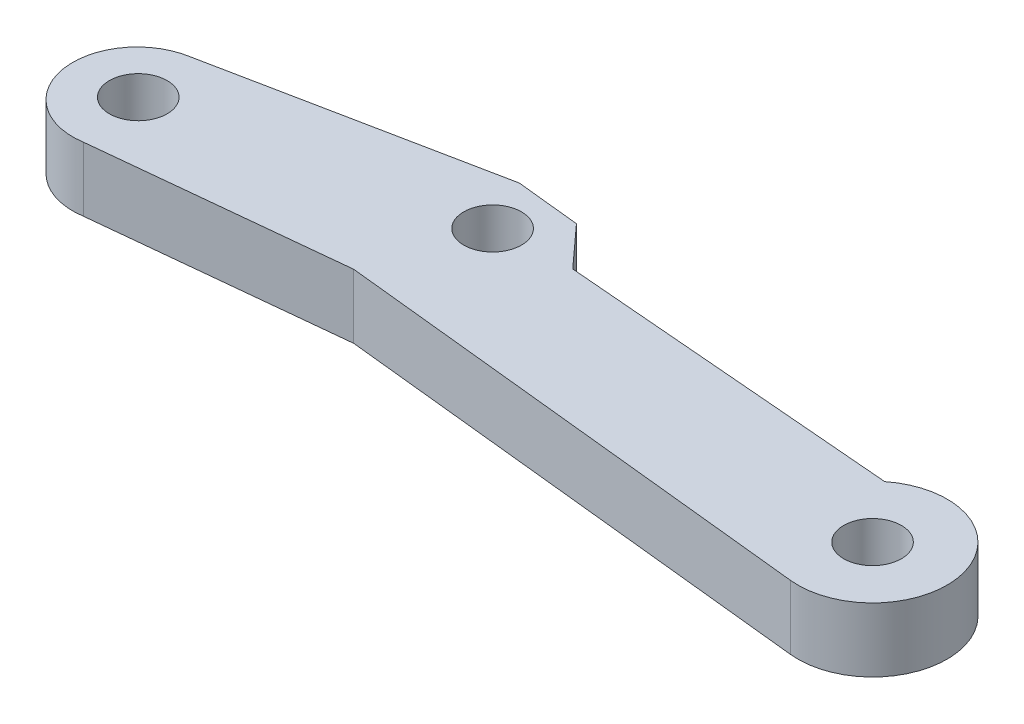
SolidWorks part; units mm, degrees
ref_plane "Front Plane" through (0, 0, 0) normal (0, 0, 1) x (1, 0, 0)
ref_plane "Top Plane" through (0, 0, 0) normal (0, 1, 0) x (1, 0, 0)
ref_plane "Right Plane" through (0, 0, 0) normal (1, 0, 0) x (0, 0, -1)
ref_plane "Plane1" through (0, -73, 0) normal (0, -1, 0) x (1, 0, 0)
sketch "Sketch1" plane through (0, -73, 0) normal (0, -1, 0) x (1, 0, 0)
  line L0 (47.4017, 28.4646) -> (51.4864, 32.9523)
  line L2 (51.4864, 32.9523) -> (77.9855, 35.1432)
  line L5 (80.9887, 45.4779) -> (42.9663, 41.5017)
  line L6 (42.9663, 41.5017) -> (23.8773, 43.4538)
  line L7 (22.2994, 33.525) -> (47.4017, 28.4646)
  arc A1 (23.8773, 43.4538) -> (22.2994, 33.525) centre (23.0884, 38.4894) ccw
  arc A2 (80.9887, 45.4779) -> (77.9855, 35.1432) centre (81.5931, 39.6986) cw
  dimension "D1" = 58.5047
  dimension "D2" = 5.8109
  dimension "D3" = 5.0267
extrude "Boss-Extrude1" add sketch "Sketch1" against normal blind 5
hole_wizard "Ø4.5 (4.5) Diameter Hole1" positions "Sketch15" profile "Sketch14" hole size "Ø4.5" standard "ANSI Metric" end condition through all
sketch "Sketch15" plane through (0, -73, 0) normal (0, -1, 0) x (-1, 0, 0)
  point P0 (-45.6293, -33.3389)
sketch "Sketch14" plane through (45.6293, -73, 33.3389) normal (1, 0, 0) x (0, 0, -1)
  line L0 (0, 0) -> (0, 5)
  line L1 (0, 5) -> (2.25, 5)
  line L2 (2.25, 5) -> (2.25, 0)
  line L5 (2.25, 0) -> (0, 0)
  line L11 (0, -6.35) -> (0, 107.95) construction
  dimension "Thru Hole Dia." = 4.5
  dimension "Thru Hole Depth" = 5
hole_wizard "Ø4.5 (4.5) Diameter Hole2" positions "Sketch17" profile "Sketch16" hole size "Ø4.5" standard "ANSI Metric" end condition through all
sketch "Sketch17" plane through (0, -73, 0) normal (0, -1, 0) x (-1, 0, 0)
  point P0 (-22.9657, -38.2849)
sketch "Sketch16" plane through (22.9657, -73, 38.2849) normal (1, 0, 0) x (0, 0, -1)
  line L0 (0, 0) -> (0, 5)
  line L1 (0, 5) -> (2.25, 5)
  line L2 (2.25, 5) -> (2.25, 0)
  line L5 (2.25, 0) -> (0, 0)
  line L11 (0, -6.35) -> (0, 107.95) construction
  dimension "Thru Hole Dia." = 4.5
  dimension "Thru Hole Depth" = 5
chamfer "Chamfer3" distance 1.7376 angle 41.721 1 edges at (47.4017, -70.5, 28.4646)
sketch "Sketch18" plane through (0, -68, 0) normal (0, 1, 0) x (1, 0, 0)
  circle A0 centre (81.5931, -39.6986) radius 2.25
  dimension "D1" = 4.5
extrude "Cut-Extrude1" cut sketch "Sketch18" against normal blind 10
